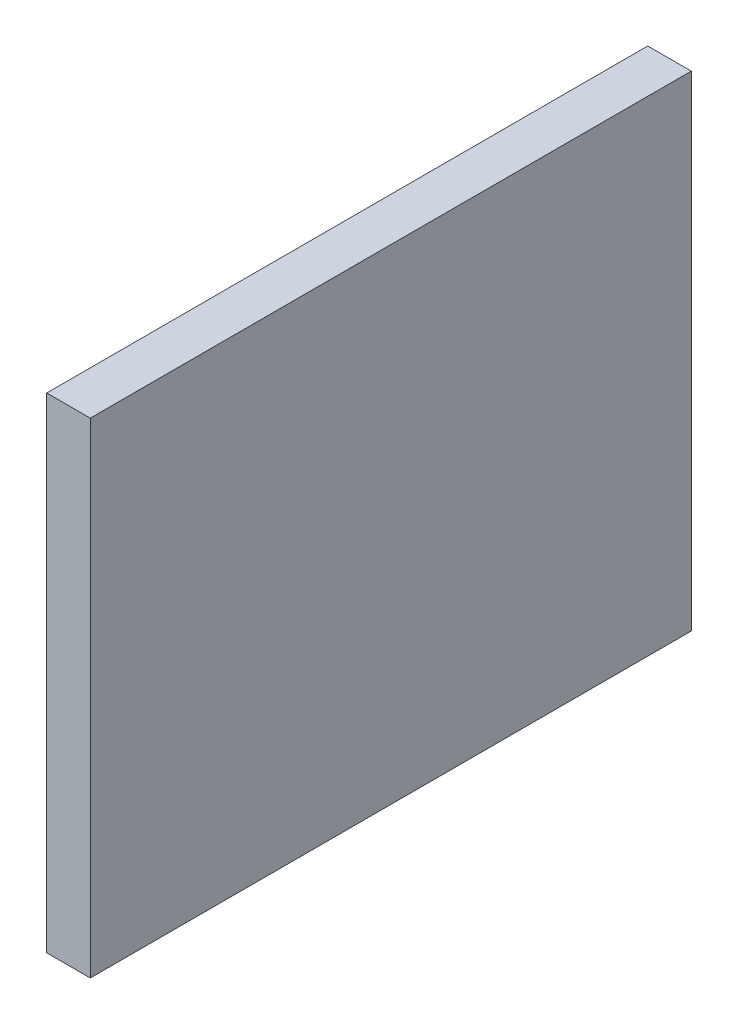
SolidWorks part; units mm, degrees
ref_plane "Alzado" through (0, 0, 0) normal (0, 0, 1) x (1, 0, 0)
ref_plane "Planta" through (0, 0, 0) normal (0, 1, 0) x (1, 0, 0)
ref_plane "Vista lateral" through (0, 0, 0) normal (1, 0, 0) x (0, 0, -1)
sketch "Croquis1" plane through (0, 0, 0) normal (1, 0, 0) x (0, 0, -1)
  line L0 (-17.3855, -31.2837) -> (24.0145, -31.2837)
  line L1 (24.0145, -31.2837) -> (24.0145, 2.1163)
  line L2 (24.0145, 2.1163) -> (-17.3855, 2.1163)
  line L3 (-17.3855, 2.1163) -> (-17.3855, -31.2837)
extrude "Saliente-Extruir1" add sketch "Croquis1" along normal blind 3
